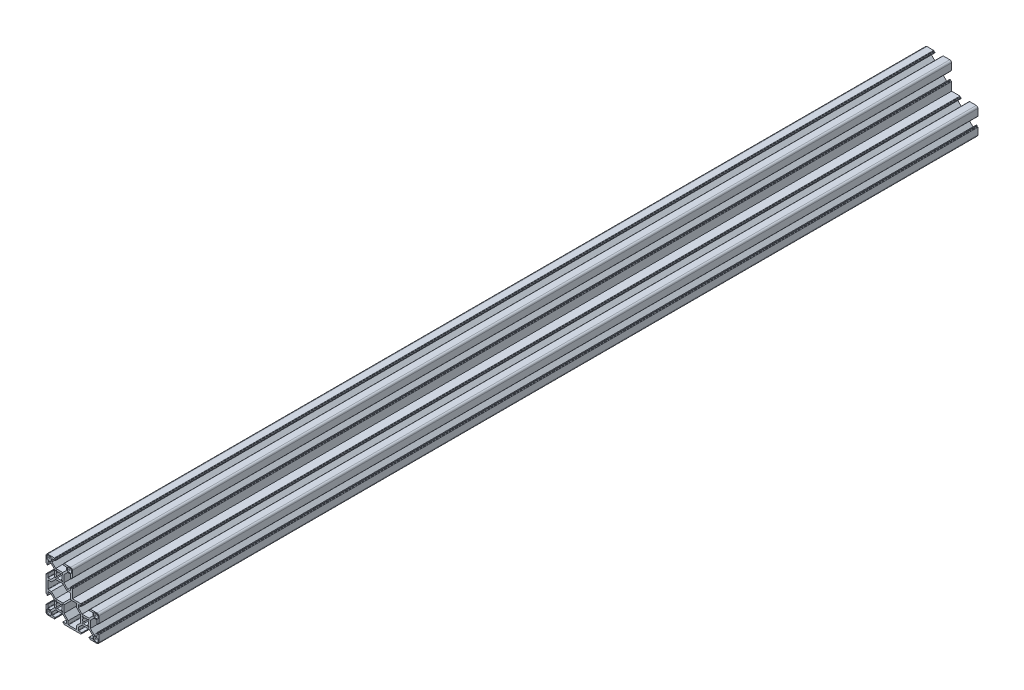
SolidWorks part; units mm, degrees
material "6063 T5"
ref_plane "Спереди" through (0, 0, 0) normal (0, 0, 1) x (1, 0, 0)
ref_plane "Сверху" through (0, 0, 0) normal (0, 1, 0) x (1, 0, 0)
ref_plane "Справа" through (0, 0, 0) normal (1, 0, 0) x (0, 0, -1)
sketch "Эскиз1" plane through (0, 0, 0) normal (0, 0, 1) x (1, 0, 0)
  line L0 (-14.9891, 50.0924) -> (45.0109, 50.0924) construction
  line L1 (0, 30) -> (0, 0) construction
  line L2 (0, 0) -> (30, 0) construction
  line L3 (-15, 38.25) -> (-15, 43)
  line L4 (-13, 45) -> (-8.25, 45)
  line L7 (-13.15, 43.95) -> (-10.05, 43.95)
  line L8 (-13.95, 43.15) -> (-13.95, 40.05)
  line L9 (-13.15, 39.25) -> (-10.05, 39.25)
  line L10 (-9.25, 43.15) -> (-9.25, 40.05)
  line L11 (13, 45) -> (8.25, 45)
  line L12 (15, 38.25) -> (15, 43)
  line L13 (13.15, 43.95) -> (10.05, 43.95)
  line L14 (13.95, 43.15) -> (13.95, 40.05)
  line L15 (13.15, 39.25) -> (10.05, 39.25)
  line L16 (9.25, 43.15) -> (9.25, 40.05)
  line L17 (0, 15) -> (-23.8455, 15) construction
  line L18 (-15, 21.75) -> (-15, 8.25)
  line L19 (15, 21.75) -> (15, 15)
  line L20 (15, 15) -> (21.75, 15)
  line L21 (8.25, -15) -> (21.75, -15)
  line L22 (-13.15, -13.95) -> (-10.05, -13.95)
  line L23 (-13.95, -13.15) -> (-13.95, -10.05)
  line L24 (-13.15, -9.25) -> (-10.05, -9.25)
  line L25 (-9.25, -13.15) -> (-9.25, -10.05)
  line L26 (-13, -15) -> (-8.25, -15)
  line L27 (-15, -8.25) -> (-15, -13)
  line L28 (15, 0) -> (15, -23.5964) construction
  line L29 (43, -15) -> (38.25, -15)
  line L30 (45, -8.25) -> (45, -13)
  line L31 (43.95, -13.15) -> (43.95, -10.05)
  line L32 (43.15, -13.95) -> (40.05, -13.95)
  line L33 (39.25, -13.15) -> (39.25, -10.05)
  line L34 (43.15, -9.25) -> (40.05, -9.25)
  line L35 (43.15, 13.95) -> (40.05, 13.95)
  line L36 (39.25, 13.15) -> (39.25, 10.05)
  line L37 (43.15, 9.25) -> (40.05, 9.25)
  line L38 (43.95, 13.15) -> (43.95, 10.05)
  line L39 (43, 15) -> (38.25, 15)
  line L40 (45, 8.25) -> (45, 13)
  line L41 (-13, 10.6) -> (-13, 19.4)
  line L42 (-12.7, 19.7) -> (-8.8716, 19.7)
  line L43 (-8.8716, 19.7) -> (-4.0716, 24.5)
  line L44 (-4.0716, 24.5) -> (4.0716, 24.5)
  line L45 (8.8716, 19.7) -> (4.0716, 24.5)
  line L46 (12.7, 19.7) -> (8.8716, 19.7)
  line L47 (13, 15) -> (13, 19.4)
  line L48 (-12.7, 10.3) -> (-8.8716, 10.3)
  line L49 (-8.8716, 10.3) -> (-4.0716, 5.5)
  line L50 (-4.0716, 5.5) -> (4.3, 5.5)
  line L51 (0, 0) -> (13, 13) construction
  line L52 (13, 15) -> (13, 13)
  line L53 (4.3, 5.5) -> (5.5, 4.3)
  line L54 (15, 13) -> (13, 13)
  line L55 (15, 13) -> (19.4, 13)
  line L56 (19.7, 12.7) -> (19.7, 8.8716)
  line L57 (19.7, 8.8716) -> (24.5, 4.0716)
  line L58 (24.5, -4.0716) -> (24.5, 4.0716)
  line L59 (19.7, -8.8716) -> (24.5, -4.0716)
  line L60 (19.7, -12.7) -> (19.7, -8.8716)
  line L61 (10.6, -13) -> (19.4, -13)
  line L62 (10.3, -12.7) -> (10.3, -8.8716)
  line L63 (10.3, -8.8716) -> (5.5, -4.0716)
  line L64 (5.5, -4.0716) -> (5.5, 4.3)
  arc A0 (-15, 43) -> (-13, 45) centre (-13, 43) cw
  arc A1 (-13.95, 40.05) -> (-13.15, 39.25) centre (-13.15, 40.05) ccw
  arc A2 (-10.05, 39.25) -> (-9.25, 40.05) centre (-10.05, 40.05) ccw
  arc A3 (-10.05, 43.95) -> (-9.25, 43.15) centre (-10.05, 43.15) cw
  arc A4 (-13.15, 43.95) -> (-13.95, 43.15) centre (-13.15, 43.15) ccw
  arc A5 (15, 43) -> (13, 45) centre (13, 43) ccw
  arc A6 (10.05, 43.95) -> (9.25, 43.15) centre (10.05, 43.15) ccw
  arc A7 (13.15, 43.95) -> (13.95, 43.15) centre (13.15, 43.15) cw
  arc A8 (13.95, 40.05) -> (13.15, 39.25) centre (13.15, 40.05) cw
  arc A9 (10.05, 39.25) -> (9.25, 40.05) centre (10.05, 40.05) cw
  arc A10 (-10.05, -13.95) -> (-9.25, -13.15) centre (-10.05, -13.15) ccw
  arc A11 (-13.15, -13.95) -> (-13.95, -13.15) centre (-13.15, -13.15) cw
  arc A12 (-13.95, -10.05) -> (-13.15, -9.25) centre (-13.15, -10.05) cw
  arc A13 (-10.05, -9.25) -> (-9.25, -10.05) centre (-10.05, -10.05) cw
  arc A14 (-15, -13) -> (-13, -15) centre (-13, -13) ccw
  arc A15 (45, -13) -> (43, -15) centre (43, -13) cw
  arc A16 (43.95, -10.05) -> (43.15, -9.25) centre (43.15, -10.05) ccw
  arc A17 (43.15, -13.95) -> (43.95, -13.15) centre (43.15, -13.15) ccw
  arc A18 (40.05, -13.95) -> (39.25, -13.15) centre (40.05, -13.15) cw
  arc A19 (40.05, -9.25) -> (39.25, -10.05) centre (40.05, -10.05) ccw
  arc A20 (43.15, 13.95) -> (43.95, 13.15) centre (43.15, 13.15) cw
  arc A21 (40.05, 13.95) -> (39.25, 13.15) centre (40.05, 13.15) ccw
  arc A22 (40.05, 9.25) -> (39.25, 10.05) centre (40.05, 10.05) cw
  arc A23 (43.95, 10.05) -> (43.15, 9.25) centre (43.15, 10.05) cw
  arc A24 (45, 13) -> (43, 15) centre (43, 13) ccw
  arc A25 (-13, 19.4) -> (-12.7, 19.7) centre (-12.7, 19.4) cw
  arc A26 (13, 19.4) -> (12.7, 19.7) centre (12.7, 19.4) ccw
  arc A27 (-13, 10.6) -> (-12.7, 10.3) centre (-12.7, 10.6) ccw
  arc A28 (19.4, 13) -> (19.7, 12.7) centre (19.4, 12.7) cw
  arc A29 (19.4, -13) -> (19.7, -12.7) centre (19.4, -12.7) ccw
  arc A30 (10.6, -13) -> (10.3, -12.7) centre (10.6, -12.7) cw
  point P2 (0, 30)
  point P7 (30, 0)
  point P22 (-9.25, 43.95)
  point P25 (-13.95, 43.95)
  point P113 (-13, 19.7)
  point P118 (0, 24.5)
  point P123 (-13, 15)
  point P145 (4.9, 4.9)
  line B0 (-15, 38.25) -> (-15, 35.5)
  line B1 (-14.7, 35.2) -> (-14.3, 35.2)
  line B2 (-14, 34.9) -> (-14, 34.4)
  line B3 (-13.7, 34.1) -> (-13.3, 34.1)
  line B4 (-13, 34.4) -> (-13, 37.95)
  line B5 (-12.7, 38.25) -> (-9.65, 38.25)
  line B6 (-9.65, 38.25) -> (-5.4, 34)
  line B7 (-5.4, 30) -> (-15, 30) construction
  line B8 (-5.4, 26) -> (-5.4, 34)
  line B9 (-9.65, 21.75) -> (-5.4, 26)
  line B10 (-12.7, 21.75) -> (-9.65, 21.75)
  line B11 (-13, 25.6) -> (-13, 22.05)
  line B12 (-13.7, 25.9) -> (-13.3, 25.9)
  line B13 (-14, 25.1) -> (-14, 25.6)
  line B14 (-14.7, 24.8) -> (-14.3, 24.8)
  line B15 (-15, 21.75) -> (-15, 24.5)
  arc B16 (-13, 37.95) -> (-12.7, 38.25) centre (-12.7, 37.95) cw
  arc B17 (-13.3, 34.1) -> (-13, 34.4) centre (-13.3, 34.4) ccw
  arc B18 (-14, 34.4) -> (-13.7, 34.1) centre (-13.7, 34.4) ccw
  arc B19 (-14.3, 35.2) -> (-14, 34.9) centre (-14.3, 34.9) cw
  arc B20 (-15, 35.5) -> (-14.7, 35.2) centre (-14.7, 35.5) ccw
  arc B21 (-15, 24.5) -> (-14.7, 24.8) centre (-14.7, 24.5) cw
  arc B22 (-14.3, 24.8) -> (-14, 25.1) centre (-14.3, 25.1) ccw
  arc B23 (-14, 25.6) -> (-13.7, 25.9) centre (-13.7, 25.6) cw
  arc B24 (-13.3, 25.9) -> (-13, 25.6) centre (-13.3, 25.6) cw
  arc B25 (-13, 22.05) -> (-12.7, 21.75) centre (-12.7, 22.05) ccw
  line B26 (0, 30) -> (3.4648, 33.4648) construction
  line B27 (0, 30) -> (0, 33.4) construction
  line B28 (0, 30) -> (3.4, 30) construction
  line B29 (3.0759, 33.8537) -> (1.9836, 32.7614)
  line B30 (3.8537, 33.0759) -> (2.7614, 31.9836)
  line B31 (-3.0759, 33.8537) -> (-1.9836, 32.7614)
  line B32 (-3.8537, 33.0759) -> (-2.7614, 31.9836)
  line B33 (-3.8537, 26.9241) -> (-2.7614, 28.0164)
  line B34 (-3.0759, 26.1463) -> (-1.9836, 27.2386)
  line B35 (3.0759, 26.1463) -> (1.9836, 27.2386)
  line B36 (3.8537, 26.9241) -> (2.7614, 28.0164)
  arc B37 (2.7614, 28.0164) -> (2.7614, 31.9836) centre (0, 30) ccw
  arc B38 (3.0759, 33.8537) -> (3.8537, 33.0759) centre (3.4648, 33.4648) cw
  arc B39 (1.9836, 32.7614) -> (-1.9836, 32.7614) centre (0, 30) ccw
  arc B40 (-3.0759, 33.8537) -> (-3.8537, 33.0759) centre (-3.4648, 33.4648) ccw
  arc B41 (-2.7614, 28.0164) -> (-2.7614, 31.9836) centre (0, 30) cw
  arc B42 (-3.0759, 26.1463) -> (-3.8537, 26.9241) centre (-3.4648, 26.5352) cw
  arc B43 (1.9836, 27.2386) -> (-1.9836, 27.2386) centre (0, 30) cw
  arc B44 (3.0759, 26.1463) -> (3.8537, 26.9241) centre (3.4648, 26.5352) ccw
  line B45 (0, 0) -> (3.4648, 3.4648) construction
  line B46 (0, 0) -> (0, 3.4) construction
  line B47 (0, 0) -> (3.4, 0) construction
  line B48 (3.0759, 3.8537) -> (1.9836, 2.7614)
  line B49 (3.8537, 3.0759) -> (2.7614, 1.9836)
  line B50 (-3.0759, 3.8537) -> (-1.9836, 2.7614)
  line B51 (-3.8537, 3.0759) -> (-2.7614, 1.9836)
  line B52 (-3.8537, -3.0759) -> (-2.7614, -1.9836)
  line B53 (-3.0759, -3.8537) -> (-1.9836, -2.7614)
  line B54 (3.0759, -3.8537) -> (1.9836, -2.7614)
  line B55 (3.8537, -3.0759) -> (2.7614, -1.9836)
  arc B56 (2.7614, -1.9836) -> (2.7614, 1.9836) centre (0, 0) ccw
  arc B57 (3.0759, 3.8537) -> (3.8537, 3.0759) centre (3.4648, 3.4648) cw
  arc B58 (1.9836, 2.7614) -> (-1.9836, 2.7614) centre (0, 0) ccw
  arc B59 (-3.0759, 3.8537) -> (-3.8537, 3.0759) centre (-3.4648, 3.4648) ccw
  arc B60 (-2.7614, -1.9836) -> (-2.7614, 1.9836) centre (0, 0) cw
  arc B61 (-3.0759, -3.8537) -> (-3.8537, -3.0759) centre (-3.4648, -3.4648) cw
  arc B62 (1.9836, -2.7614) -> (-1.9836, -2.7614) centre (0, 0) cw
  arc B63 (3.0759, -3.8537) -> (3.8537, -3.0759) centre (3.4648, -3.4648) ccw
  line B64 (30, 0) -> (33.4648, 3.4648) construction
  line B65 (30, 0) -> (30, 3.4) construction
  line B66 (30, 0) -> (33.4, 0) construction
  line B67 (33.0759, 3.8537) -> (31.9836, 2.7614)
  line B68 (33.8537, 3.0759) -> (32.7614, 1.9836)
  line B69 (26.9241, 3.8537) -> (28.0164, 2.7614)
  line B70 (26.1463, 3.0759) -> (27.2386, 1.9836)
  line B71 (26.1463, -3.0759) -> (27.2386, -1.9836)
  line B72 (26.9241, -3.8537) -> (28.0164, -2.7614)
  line B73 (33.0759, -3.8537) -> (31.9836, -2.7614)
  line B74 (33.8537, -3.0759) -> (32.7614, -1.9836)
  arc B75 (32.7614, -1.9836) -> (32.7614, 1.9836) centre (30, 0) ccw
  arc B76 (33.0759, 3.8537) -> (33.8537, 3.0759) centre (33.4648, 3.4648) cw
  arc B77 (31.9836, 2.7614) -> (28.0164, 2.7614) centre (30, 0) ccw
  arc B78 (26.9241, 3.8537) -> (26.1463, 3.0759) centre (26.5352, 3.4648) ccw
  arc B79 (27.2386, -1.9836) -> (27.2386, 1.9836) centre (30, 0) cw
  arc B80 (26.9241, -3.8537) -> (26.1463, -3.0759) centre (26.5352, -3.4648) cw
  arc B81 (31.9836, -2.7614) -> (28.0164, -2.7614) centre (30, 0) cw
  arc B82 (33.0759, -3.8537) -> (33.8537, -3.0759) centre (33.4648, -3.4648) ccw
  line B83 (8.25, 45) -> (5.5, 45)
  line B84 (5.2, 44.7) -> (5.2, 44.3)
  line B85 (4.9, 44) -> (4.4, 44)
  line B86 (4.1, 43.7) -> (4.1, 43.3)
  line B87 (4.4, 43) -> (7.95, 43)
  line B88 (8.25, 42.7) -> (8.25, 39.65)
  line B89 (8.25, 39.65) -> (4, 35.4)
  line B90 (0, 35.4) -> (0, 45) construction
  line B91 (-4, 35.4) -> (4, 35.4)
  line B92 (-8.25, 39.65) -> (-4, 35.4)
  line B93 (-8.25, 42.7) -> (-8.25, 39.65)
  line B94 (-4.4, 43) -> (-7.95, 43)
  line B95 (-4.1, 43.7) -> (-4.1, 43.3)
  line B96 (-4.9, 44) -> (-4.4, 44)
  line B97 (-5.2, 44.7) -> (-5.2, 44.3)
  line B98 (-8.25, 45) -> (-5.5, 45)
  arc B99 (7.95, 43) -> (8.25, 42.7) centre (7.95, 42.7) cw
  arc B100 (4.1, 43.3) -> (4.4, 43) centre (4.4, 43.3) ccw
  arc B101 (4.4, 44) -> (4.1, 43.7) centre (4.4, 43.7) ccw
  arc B102 (5.2, 44.3) -> (4.9, 44) centre (4.9, 44.3) cw
  arc B103 (5.5, 45) -> (5.2, 44.7) centre (5.5, 44.7) ccw
  arc B104 (-5.5, 45) -> (-5.2, 44.7) centre (-5.5, 44.7) cw
  arc B105 (-5.2, 44.3) -> (-4.9, 44) centre (-4.9, 44.3) ccw
  arc B106 (-4.4, 44) -> (-4.1, 43.7) centre (-4.4, 43.7) cw
  arc B107 (-4.1, 43.3) -> (-4.4, 43) centre (-4.4, 43.3) cw
  arc B108 (-7.95, 43) -> (-8.25, 42.7) centre (-7.95, 42.7) ccw
  line B109 (15, 21.75) -> (15, 24.5)
  line B110 (14.7, 24.8) -> (14.3, 24.8)
  line B111 (14, 25.1) -> (14, 25.6)
  line B112 (13.7, 25.9) -> (13.3, 25.9)
  line B113 (13, 25.6) -> (13, 22.05)
  line B114 (12.7, 21.75) -> (9.65, 21.75)
  line B115 (9.65, 21.75) -> (5.4, 26)
  line B116 (5.4, 30) -> (15, 30) construction
  line B117 (5.4, 34) -> (5.4, 26)
  line B118 (9.65, 38.25) -> (5.4, 34)
  line B119 (12.7, 38.25) -> (9.65, 38.25)
  line B120 (13, 34.4) -> (13, 37.95)
  line B121 (13.7, 34.1) -> (13.3, 34.1)
  line B122 (14, 34.9) -> (14, 34.4)
  line B123 (14.7, 35.2) -> (14.3, 35.2)
  line B124 (15, 38.25) -> (15, 35.5)
  arc B125 (13, 22.05) -> (12.7, 21.75) centre (12.7, 22.05) cw
  arc B126 (13.3, 25.9) -> (13, 25.6) centre (13.3, 25.6) ccw
  arc B127 (14, 25.6) -> (13.7, 25.9) centre (13.7, 25.6) ccw
  arc B128 (14.3, 24.8) -> (14, 25.1) centre (14.3, 25.1) cw
  arc B129 (15, 24.5) -> (14.7, 24.8) centre (14.7, 24.5) ccw
  arc B130 (15, 35.5) -> (14.7, 35.2) centre (14.7, 35.5) cw
  arc B131 (14.3, 35.2) -> (14, 34.9) centre (14.3, 34.9) ccw
  arc B132 (14, 34.4) -> (13.7, 34.1) centre (13.7, 34.4) cw
  arc B133 (13.3, 34.1) -> (13, 34.4) centre (13.3, 34.4) cw
  arc B134 (13, 37.95) -> (12.7, 38.25) centre (12.7, 37.95) ccw
  line B135 (-15, 8.25) -> (-15, 5.5)
  line B136 (-14.7, 5.2) -> (-14.3, 5.2)
  line B137 (-14, 4.9) -> (-14, 4.4)
  line B138 (-13.7, 4.1) -> (-13.3, 4.1)
  line B139 (-13, 4.4) -> (-13, 7.95)
  line B140 (-12.7, 8.25) -> (-9.65, 8.25)
  line B141 (-9.65, 8.25) -> (-5.4, 4)
  line B142 (-5.4, 0) -> (-15, 0) construction
  line B143 (-5.4, -4) -> (-5.4, 4)
  line B144 (-9.65, -8.25) -> (-5.4, -4)
  line B145 (-12.7, -8.25) -> (-9.65, -8.25)
  line B146 (-13, -4.4) -> (-13, -7.95)
  line B147 (-13.7, -4.1) -> (-13.3, -4.1)
  line B148 (-14, -4.9) -> (-14, -4.4)
  line B149 (-14.7, -5.2) -> (-14.3, -5.2)
  line B150 (-15, -8.25) -> (-15, -5.5)
  arc B151 (-13, 7.95) -> (-12.7, 8.25) centre (-12.7, 7.95) cw
  arc B152 (-13.3, 4.1) -> (-13, 4.4) centre (-13.3, 4.4) ccw
  arc B153 (-14, 4.4) -> (-13.7, 4.1) centre (-13.7, 4.4) ccw
  arc B154 (-14.3, 5.2) -> (-14, 4.9) centre (-14.3, 4.9) cw
  arc B155 (-15, 5.5) -> (-14.7, 5.2) centre (-14.7, 5.5) ccw
  arc B156 (-15, -5.5) -> (-14.7, -5.2) centre (-14.7, -5.5) cw
  arc B157 (-14.3, -5.2) -> (-14, -4.9) centre (-14.3, -4.9) ccw
  arc B158 (-14, -4.4) -> (-13.7, -4.1) centre (-13.7, -4.4) cw
  arc B159 (-13.3, -4.1) -> (-13, -4.4) centre (-13.3, -4.4) cw
  arc B160 (-13, -7.95) -> (-12.7, -8.25) centre (-12.7, -7.95) ccw
  line B161 (-8.25, -15) -> (-5.5, -15)
  line B162 (-5.2, -14.7) -> (-5.2, -14.3)
  line B163 (-4.9, -14) -> (-4.4, -14)
  line B164 (-4.1, -13.7) -> (-4.1, -13.3)
  line B165 (-4.4, -13) -> (-7.95, -13)
  line B166 (-8.25, -12.7) -> (-8.25, -9.65)
  line B167 (-8.25, -9.65) -> (-4, -5.4)
  line B168 (0, -5.4) -> (0, -15) construction
  line B169 (4, -5.4) -> (-4, -5.4)
  line B170 (8.25, -9.65) -> (4, -5.4)
  line B171 (8.25, -12.7) -> (8.25, -9.65)
  line B172 (4.4, -13) -> (7.95, -13)
  line B173 (4.1, -13.7) -> (4.1, -13.3)
  line B174 (4.9, -14) -> (4.4, -14)
  line B175 (5.2, -14.7) -> (5.2, -14.3)
  line B176 (8.25, -15) -> (5.5, -15)
  arc B177 (-7.95, -13) -> (-8.25, -12.7) centre (-7.95, -12.7) cw
  arc B178 (-4.1, -13.3) -> (-4.4, -13) centre (-4.4, -13.3) ccw
  arc B179 (-4.4, -14) -> (-4.1, -13.7) centre (-4.4, -13.7) ccw
  arc B180 (-5.2, -14.3) -> (-4.9, -14) centre (-4.9, -14.3) cw
  arc B181 (-5.5, -15) -> (-5.2, -14.7) centre (-5.5, -14.7) ccw
  arc B182 (5.5, -15) -> (5.2, -14.7) centre (5.5, -14.7) cw
  arc B183 (5.2, -14.3) -> (4.9, -14) centre (4.9, -14.3) ccw
  arc B184 (4.4, -14) -> (4.1, -13.7) centre (4.4, -13.7) cw
  arc B185 (4.1, -13.3) -> (4.4, -13) centre (4.4, -13.3) cw
  arc B186 (7.95, -13) -> (8.25, -12.7) centre (7.95, -12.7) ccw
  line B187 (38.25, 15) -> (35.5, 15)
  line B188 (35.2, 14.7) -> (35.2, 14.3)
  line B189 (34.9, 14) -> (34.4, 14)
  line B190 (34.1, 13.7) -> (34.1, 13.3)
  line B191 (34.4, 13) -> (37.95, 13)
  line B192 (38.25, 12.7) -> (38.25, 9.65)
  line B193 (38.25, 9.65) -> (34, 5.4)
  line B194 (30, 5.4) -> (30, 15) construction
  line B195 (26, 5.4) -> (34, 5.4)
  line B196 (21.75, 9.65) -> (26, 5.4)
  line B197 (21.75, 12.7) -> (21.75, 9.65)
  line B198 (25.6, 13) -> (22.05, 13)
  line B199 (25.9, 13.7) -> (25.9, 13.3)
  line B200 (25.1, 14) -> (25.6, 14)
  line B201 (24.8, 14.7) -> (24.8, 14.3)
  line B202 (21.75, 15) -> (24.5, 15)
  arc B203 (37.95, 13) -> (38.25, 12.7) centre (37.95, 12.7) cw
  arc B204 (34.1, 13.3) -> (34.4, 13) centre (34.4, 13.3) ccw
  arc B205 (34.4, 14) -> (34.1, 13.7) centre (34.4, 13.7) ccw
  arc B206 (35.2, 14.3) -> (34.9, 14) centre (34.9, 14.3) cw
  arc B207 (35.5, 15) -> (35.2, 14.7) centre (35.5, 14.7) ccw
  arc B208 (24.5, 15) -> (24.8, 14.7) centre (24.5, 14.7) cw
  arc B209 (24.8, 14.3) -> (25.1, 14) centre (25.1, 14.3) ccw
  arc B210 (25.6, 14) -> (25.9, 13.7) centre (25.6, 13.7) cw
  arc B211 (25.9, 13.3) -> (25.6, 13) centre (25.6, 13.3) cw
  arc B212 (22.05, 13) -> (21.75, 12.7) centre (22.05, 12.7) ccw
  line B213 (45, -8.25) -> (45, -5.5)
  line B214 (44.7, -5.2) -> (44.3, -5.2)
  line B215 (44, -4.9) -> (44, -4.4)
  line B216 (43.7, -4.1) -> (43.3, -4.1)
  line B217 (43, -4.4) -> (43, -7.95)
  line B218 (42.7, -8.25) -> (39.65, -8.25)
  line B219 (39.65, -8.25) -> (35.4, -4)
  line B220 (35.4, 0) -> (45, 0) construction
  line B221 (35.4, 4) -> (35.4, -4)
  line B222 (39.65, 8.25) -> (35.4, 4)
  line B223 (42.7, 8.25) -> (39.65, 8.25)
  line B224 (43, 4.4) -> (43, 7.95)
  line B225 (43.7, 4.1) -> (43.3, 4.1)
  line B226 (44, 4.9) -> (44, 4.4)
  line B227 (44.7, 5.2) -> (44.3, 5.2)
  line B228 (45, 8.25) -> (45, 5.5)
  arc B229 (43, -7.95) -> (42.7, -8.25) centre (42.7, -7.95) cw
  arc B230 (43.3, -4.1) -> (43, -4.4) centre (43.3, -4.4) ccw
  arc B231 (44, -4.4) -> (43.7, -4.1) centre (43.7, -4.4) ccw
  arc B232 (44.3, -5.2) -> (44, -4.9) centre (44.3, -4.9) cw
  arc B233 (45, -5.5) -> (44.7, -5.2) centre (44.7, -5.5) ccw
  arc B234 (45, 5.5) -> (44.7, 5.2) centre (44.7, 5.5) cw
  arc B235 (44.3, 5.2) -> (44, 4.9) centre (44.3, 4.9) ccw
  arc B236 (44, 4.4) -> (43.7, 4.1) centre (43.7, 4.4) cw
  arc B237 (43.3, 4.1) -> (43, 4.4) centre (43.3, 4.4) cw
  arc B238 (43, 7.95) -> (42.7, 8.25) centre (42.7, 7.95) ccw
  line B239 (21.75, -15) -> (24.5, -15)
  line B240 (24.8, -14.7) -> (24.8, -14.3)
  line B241 (25.1, -14) -> (25.6, -14)
  line B242 (25.9, -13.7) -> (25.9, -13.3)
  line B243 (25.6, -13) -> (22.05, -13)
  line B244 (21.75, -12.7) -> (21.75, -9.65)
  line B245 (21.75, -9.65) -> (26, -5.4)
  line B246 (30, -5.4) -> (30, -15) construction
  line B247 (34, -5.4) -> (26, -5.4)
  line B248 (38.25, -9.65) -> (34, -5.4)
  line B249 (38.25, -12.7) -> (38.25, -9.65)
  line B250 (34.4, -13) -> (37.95, -13)
  line B251 (34.1, -13.7) -> (34.1, -13.3)
  line B252 (34.9, -14) -> (34.4, -14)
  line B253 (35.2, -14.7) -> (35.2, -14.3)
  line B254 (38.25, -15) -> (35.5, -15)
  arc B255 (22.05, -13) -> (21.75, -12.7) centre (22.05, -12.7) cw
  arc B256 (25.9, -13.3) -> (25.6, -13) centre (25.6, -13.3) ccw
  arc B257 (25.6, -14) -> (25.9, -13.7) centre (25.6, -13.7) ccw
  arc B258 (24.8, -14.3) -> (25.1, -14) centre (25.1, -14.3) cw
  arc B259 (24.5, -15) -> (24.8, -14.7) centre (24.5, -14.7) ccw
  arc B260 (35.5, -15) -> (35.2, -14.7) centre (35.5, -14.7) cw
  arc B261 (35.2, -14.3) -> (34.9, -14) centre (34.9, -14.3) ccw
  arc B262 (34.4, -14) -> (34.1, -13.7) centre (34.4, -13.7) cw
  arc B263 (34.1, -13.3) -> (34.4, -13) centre (34.4, -13.3) cw
  arc B264 (37.95, -13) -> (38.25, -12.7) centre (37.95, -12.7) ccw
  dimension "D3" = 15
  dimension "D6" = 2
  dimension "D10" = 0.8
  dimension "D15" = 0.3
  dimension "D1" = 60
  dimension "D2" = 30
  dimension "D4" = 15
  dimension "D5" = 15
  dimension "D7" = 1
  dimension "D8" = 1
  dimension "D9" = 4.7
  dimension "D11" = 2
  dimension "D12" = 2
  dimension "D13" = 5.5
  dimension "D14" = 4.7
  dimension "D16" = 45
  dimension "D17" = 0.6
sketch_block_instance "8B(16,5P)-1"
sketch_block "8B(16,5P)" parameters "D7"=0.3, "D1"=16.5, "D2"=2, "D3"=8, "D4"=9.6, "D5"=45, "D6"=10.4, "D8"=0.4
sketch_block_instance "Блок1-1"
sketch_block "Блок1" parameters "D2"=6.8, "D1"=45, "D3"=1.1, "D4"=4.9
sketch_block_instance "Блок1-2"
sketch_block_instance "Блок1-3"
sketch_block_instance "8B(16,5P)-3"
sketch_block_instance "8B(16,5P)-4"
sketch_block_instance "8B(16,5P)-5"
sketch_block_instance "8B(16,5P)-7"
sketch_block_instance "8B(16,5P)-8"
sketch_block_instance "8B(16,5P)-9"
sketch_block_instance "8B(16,5P)-10"
extrude "Бобышка-Вытянуть1" add sketch "Эскиз1" along normal blind 1000 contours B264 B250 B263 B251 B262 B252 B261 B253 B260 B254 L29 A15 L30 B213 B233 B214 B232 B215 B231 B216 B230 B217 B229 B218 B219 B221 B222 B223 B238 B224 B237 B225 B236 B226 B235 B227 B234 B228 L40 A24 L39 B187 B207 B188 B206 B189 B205 B190 B204 B191 B203
